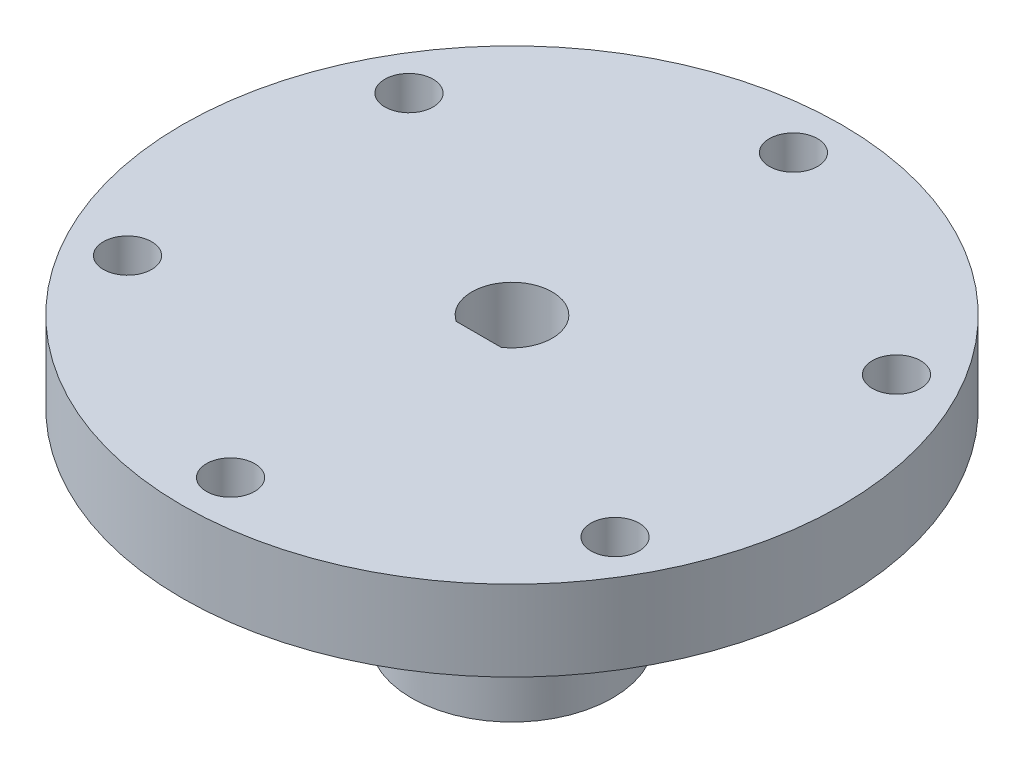
SolidWorks part; units mm, degrees
material "6061 Alloy"
ref_plane "Front Plane" through (0, 0, 0) normal (0, 0, 1) x (1, 0, 0)
ref_plane "Top Plane" through (0, 0, 0) normal (0, 1, 0) x (1, 0, 0)
ref_plane "Right Plane" through (0, 0, 0) normal (1, 0, 0) x (0, 0, -1)
sketch "Sketch1" plane through (0, 0, 0) normal (0, 1, 0) x (1, 0, 0)
  circle A0 centre (0, 0) radius 5
  circle A1 centre (0, 0) radius 12.5
  dimension "D1" = 10
  dimension "D2" = 25
extrude "Boss-Extrude1" add sketch "Sketch1" along normal blind 15
sketch "Sketch2" plane through (0, 15, 0) normal (0, 1, 0) x (1, 0, 0)
  circle A0 centre (0, 0) radius 5
  circle A1 centre (0, 0) radius 41
  circle A3 centre (0, 0) radius 5 construction
  dimension "D1" = 82
extrude "Boss-Extrude2" add sketch "Sketch2" along normal blind 20
sketch "Sketch3" plane through (0, 35, 0) normal (0, 1, 0) x (1, 0, 0)
  circle A0 centre (0, 0) radius 35 construction
  circle A1 centre (0, 35) radius 3
  circle A2 centre (30.3109, 17.5) radius 3
  circle A3 centre (30.3109, -17.5) radius 3
  circle A4 centre (0, -35) radius 3
  circle A5 centre (-30.3109, -17.5) radius 3
  circle A6 centre (-30.3109, 17.5) radius 3
  point P17 (0, 0)
  dimension "D1" = 70
  dimension "D2" = 6
  dimension "D3" = 6
extrude "Cut-Extrude1" cut sketch "Sketch3" against normal through all
sketch "Sketch4" plane through (0, 0, 0) normal (0, -1, 0) x (1, 0, 0)
  line L0 (-3.0679, 4.15) -> (3.0679, 4.15)
  circle A0 centre (0, 0) radius 5.1608
  circle M3 centre (0, 0) radius 5
  dimension "D1" = 4.15
extrude "Boss-Extrude3" add sketch "Sketch4" against normal blind 35 contours L0 M3
sketch "Sketch5" plane through (0, 0, 4.15) normal (0, 0, -1) x (-1, 0, 0)
  line L0 (0, 35) -> (0, 0) construction
  line L1 (2.7888, 35) -> (-2.7888, 35) construction
  line L2 (2.7888, 0) -> (-2.7888, 0) construction
  circle A0 centre (0, 9) radius 1.5
  dimension "D1" = 3
  dimension "D2" = 9
extrude "Cut-Extrude2" cut sketch "Sketch5" against normal through all
sketch "Sketch6" plane through (0, 15, 0) normal (0, -1, 0) x (1, 0, 0)
  circle A0 centre (0, 0) radius 12.5
  circle A1 centre (0, 0) radius 41
  circle A2 centre (0, 0) radius 41 construction
  circle A3 centre (0, 0) radius 12.5 construction
extrude "Cut-Extrude3" cut sketch "Sketch6" against normal blind 10
sketch "Sketch7" plane through (0, 35, 0) normal (0, 1, 0) x (1, 0, 0)
  circle A0 centre (-2.7888, -4.15) radius 0.7109
  circle A1 centre (2.7888, -4.15) radius 0.682
